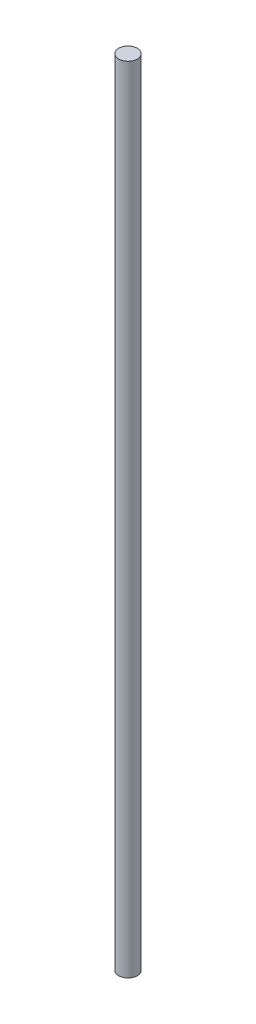
SolidWorks part; units mm, degrees
ref_plane "Front Plane" through (0, 0, 0) normal (0, 0, 1) x (1, 0, 0)
ref_plane "Top Plane" through (0, 0, 0) normal (0, 1, 0) x (1, 0, 0)
ref_plane "Right Plane" through (0, 0, 0) normal (1, 0, 0) x (0, 0, -1)
sketch "Sketch1" plane through (0, 0, 0) normal (0, 1, 0) x (1, 0, 0)
  circle A0 centre (0, 0) radius 82.5
  dimension "D1" = 165
extrude "Boss-Extrude1" add sketch "Sketch1" along normal blind 7000
